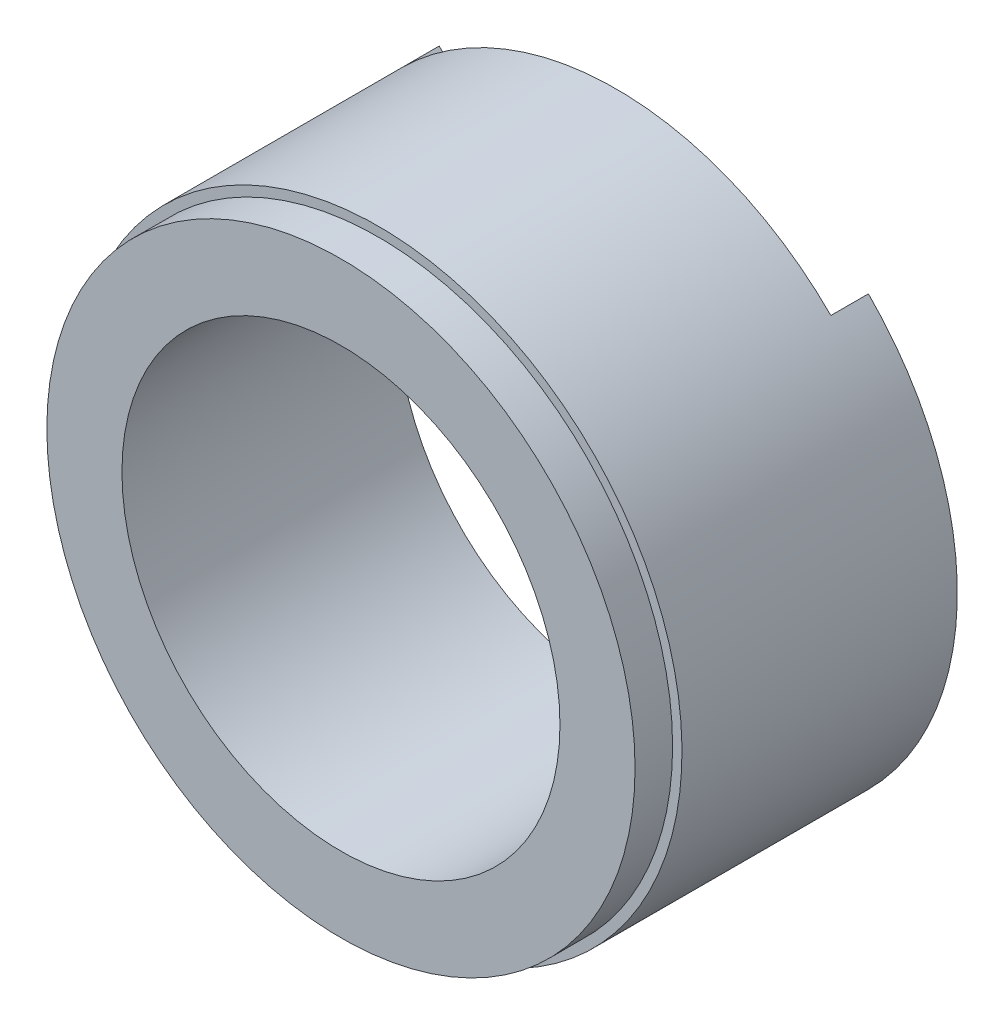
SolidWorks part; units mm, degrees
ref_plane "Plan de face" through (0, 0, 0) normal (0, 0, 1) x (1, 0, 0)
ref_plane "Plan de dessus" through (0, 0, 0) normal (0, 1, 0) x (1, 0, 0)
ref_plane "Plan de droite" through (0, 0, 0) normal (1, 0, 0) x (0, 0, -1)
sketch "Esquisse1" plane through (0, 0, 0) normal (0, 0, 1) x (1, 0, 0)
  circle A0 centre (0, 0) radius 48.5
  dimension "D1" = 97
extrude "Boss.-Extru.1" add sketch "Esquisse1" along normal blind 44
sketch "Esquisse2" plane through (0, 0, 44) normal (0, 0, 1) x (1, 0, 0)
  circle A0 centre (0, 0) radius 48.5
  circle A1 centre (0, 0) radius 47
  dimension "D1" = 94
extrude "Enlèv. mat.-Extru.1" cut sketch "Esquisse2" against normal blind 6
sketch "Esquisse3" plane through (0, 0, 44) normal (0, 0, 1) x (1, 0, 0)
  circle A0 centre (0, 0) radius 35
  dimension "D1" = 70
extrude "Enlèv. mat.-Extru.2" cut sketch "Esquisse3" against normal through all
sketch "Esquisse5" plane through (0, 0, 0) normal (0, 0, -1) x (-1, 0, 0)
  circle A0 centre (0, 0) radius 36.5
  circle A1 centre (0, 0) radius 45.5
  circle A2 centre (0, 0) radius 35 construction
  dimension "D1" = 9
  dimension "D2" = 1.5
extrude "Enlèv. mat.-Extru.3" cut sketch "Esquisse5" against normal blind 42
sketch "Esquisse6" plane through (0, 0, 0) normal (0, 0, -1) x (-1, 0, 0)
  line L5 (-10, -48.5543) -> (10, -48.5543)
  line L6 (-10, -48.5543) -> (-10, -44.3875)
  line L7 (-10, -44.3875) -> (10, -44.3875)
  line L8 (10, -48.5543) -> (10, -44.3875)
  circle A1 centre (0, 0) radius 45.5 construction
  dimension "D1" = 20
  dimension "D2" = 10
extrude "Enlèv. mat.-Extru.5" cut sketch "Esquisse6" against normal blind 42
sketch "Esquisse8" plane through (0, 0, 0) normal (0, 0, -1) x (-1, 0, 0)
  line L0 (48.5, 0) -> (-48.5, 0) construction
  line L1 (0, 0) -> (32.1734, -32.1734) construction
  line L2 (0, 0) -> (32.1734, 32.1734) construction
  line L3 (34.2947, 34.2947) -> (32.1734, 32.1734)
  line L4 (34.2947, -34.2947) -> (32.1734, -32.1734)
  line L5 (0, 0) -> (0, -36.5) construction
  line L6 (-34.2947, -34.2947) -> (-32.1734, -32.1734)
  line L7 (-34.2947, 34.2947) -> (-32.1734, 32.1734)
  circle A0 centre (0, 0) radius 48.5 construction
  circle A1 centre (0, 0) radius 45.5 construction
  arc A2 (32.1734, -32.1734) -> (32.1734, 32.1734) centre (0, 0) ccw
  arc A3 (34.2947, -34.2947) -> (34.2947, 34.2947) centre (0, 0) ccw
  circle A4 centre (0, 0) radius 36.5 construction
  arc A5 (-32.1734, -32.1734) -> (-32.1734, 32.1734) centre (0, 0) cw
  arc A6 (-34.2947, -34.2947) -> (-34.2947, 34.2947) centre (0, 0) cw
  arc M16 (10, -47.4579) -> (-10, -47.4579) centre (0, 0) ccw
  arc M18 (-10, -44.3875) -> (10, -44.3875) centre (0, 0) cw
  dimension "D1" = 45
  dimension "D2" = 45
extrude "Boss.-Extru.2" add sketch "Esquisse8" along normal blind 6 contours L4 L3 M16 M18 | A6 L7 A5 L6
